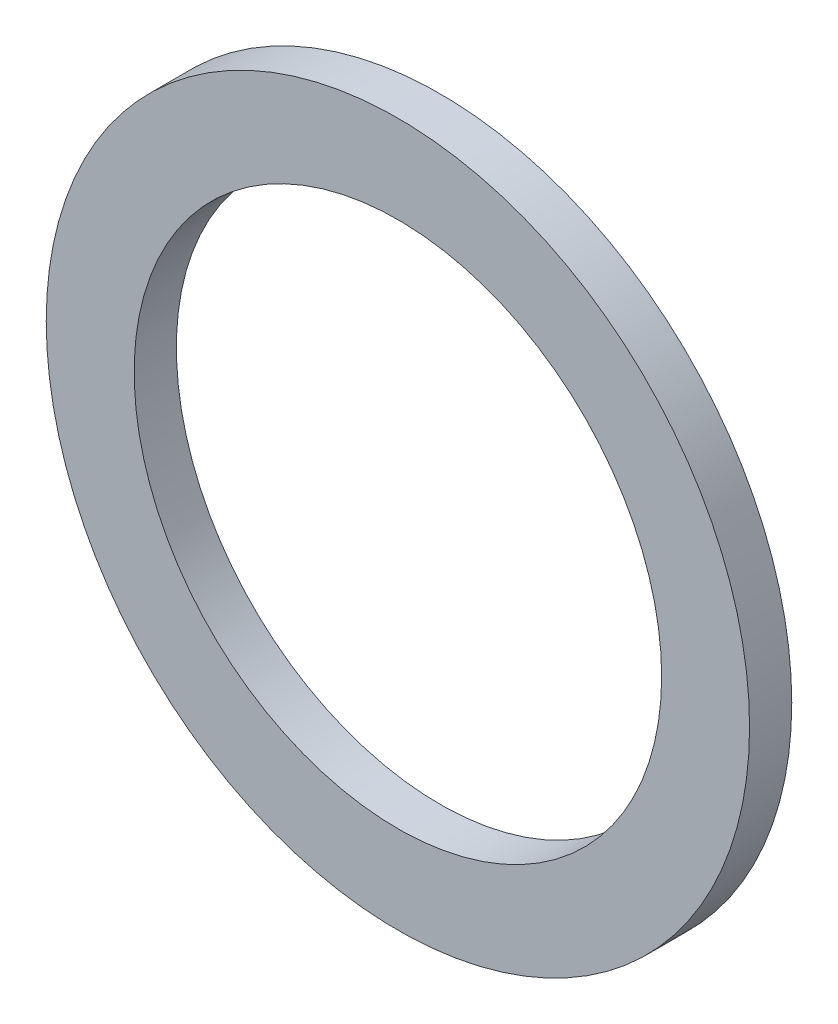
SolidWorks part; units mm, degrees
ref_plane "Front Plane" through (0, 0, 0) normal (0, 0, 1) x (1, 0, 0)
ref_plane "Top Plane" through (0, 0, 0) normal (0, 1, 0) x (1, 0, 0)
ref_plane "Right Plane" through (0, 0, 0) normal (1, 0, 0) x (0, 0, -1)
sketch "Sketch1" plane through (0, 0, 0) normal (0, 0, 1) x (1, 0, 0)
  circle A0 centre (0, 0) radius 7.5
  circle A1 centre (0, 0) radius 10
  dimension "D1" = 15
  dimension "D2" = 20
extrude "Boss-Extrude1" add sketch "Sketch1" along normal blind 1.2
